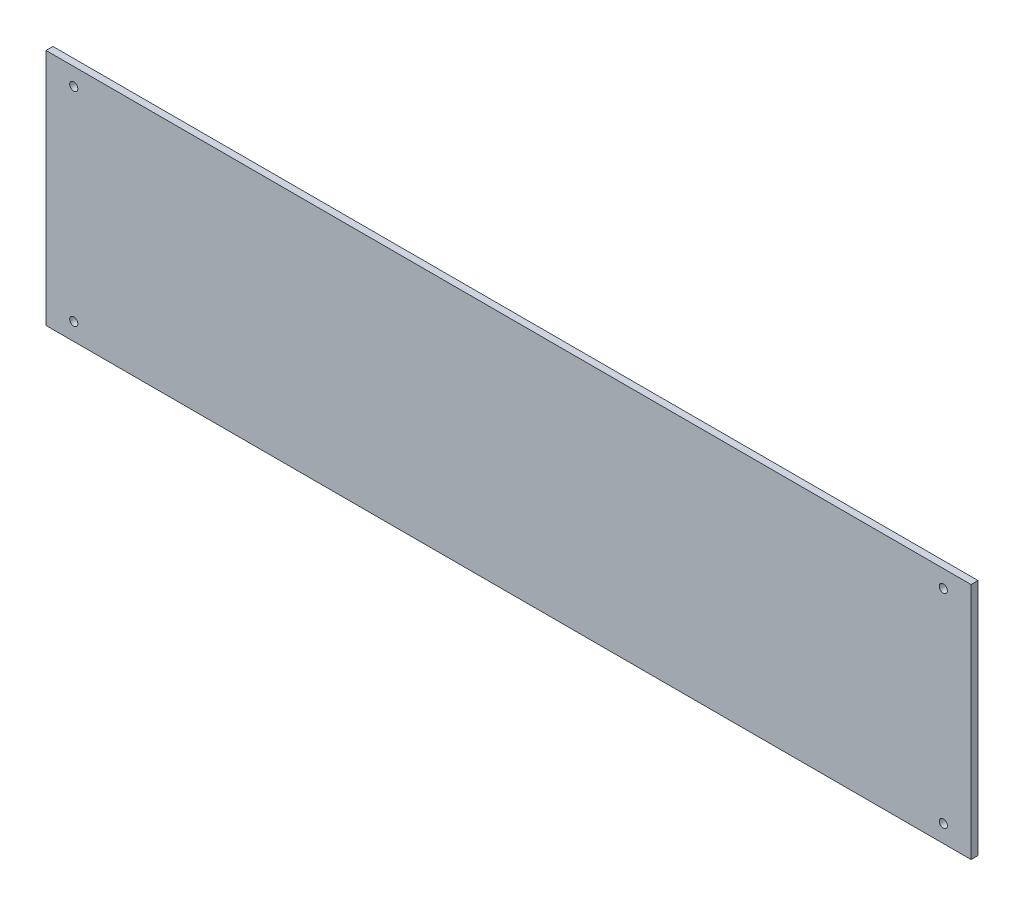
SolidWorks part; units mm, degrees
ref_plane "Front Plane" through (0, 0, 0) normal (0, 0, 1) x (1, 0, 0)
ref_plane "Top Plane" through (0, 0, 0) normal (0, 1, 0) x (1, 0, 0)
ref_plane "Right Plane" through (0, 0, 0) normal (1, 0, 0) x (0, 0, -1)
sketch "Sketch1" plane through (0, 0, 0) normal (0, 0, 1) x (1, 0, 0)
  line L1 (0, 0) -> (400, 0)
  line L2 (0, 0) -> (0, 100)
  line L3 (0, 100) -> (400, 100)
  line L4 (400, 0) -> (400, 100)
  dimension "D1" = 400
  dimension "D2" = 100
extrude "Boss-Extrude1" add sketch "Sketch1" along normal blind 3
sketch "Sketch7" plane through (0, 0, 0) normal (0, 0, -1) x (-1, 0, 0)
  line L0 (-400, 100) -> (0, 100) construction
  line L1 (-400, 0) -> (-400, 100) construction
  line L2 (0, 0) -> (-400, 0) construction
  line L3 (-200, 100) -> (-200, 78.9637) construction
  line L4 (-400, 0) -> (-400, 100) construction
  circle A0 centre (-388, 92.5) radius 1.75
  circle A1 centre (-388, 4.5) radius 1.75
  circle A2 centre (-12, 92.5) radius 1.75
  circle A3 centre (-12, 4.5) radius 1.75
  dimension "D1" = 3.5
  dimension "D5" = 3.5
  dimension "D2" = 7.5
  dimension "D3" = 12
  dimension "D4" = 4.5
  dimension "D6" = 12
extrude "Cut-Extrude6" cut sketch "Sketch7" against normal through all
sketch "Sketch8" plane through (0, 0, 0) normal (0, -1, 0) x (-1, 0, 0)
  line L0 (0, 0) -> (-400, 0) construction
  line L1 (0, 0) -> (-400, 0)
  line L2 (0, 0) -> (0, -3)
  line L3 (0, -3) -> (-400, -3)
  line L4 (-400, 0) -> (-400, -3)
  line L5 (0, -3) -> (-400, -3) construction
  line L6 (-400, -3) -> (-400, 0) construction
  line L7 (0, -3) -> (0, 0) construction
extrude "Boss-Extrude2" add sketch "Sketch8" along normal blind 3
